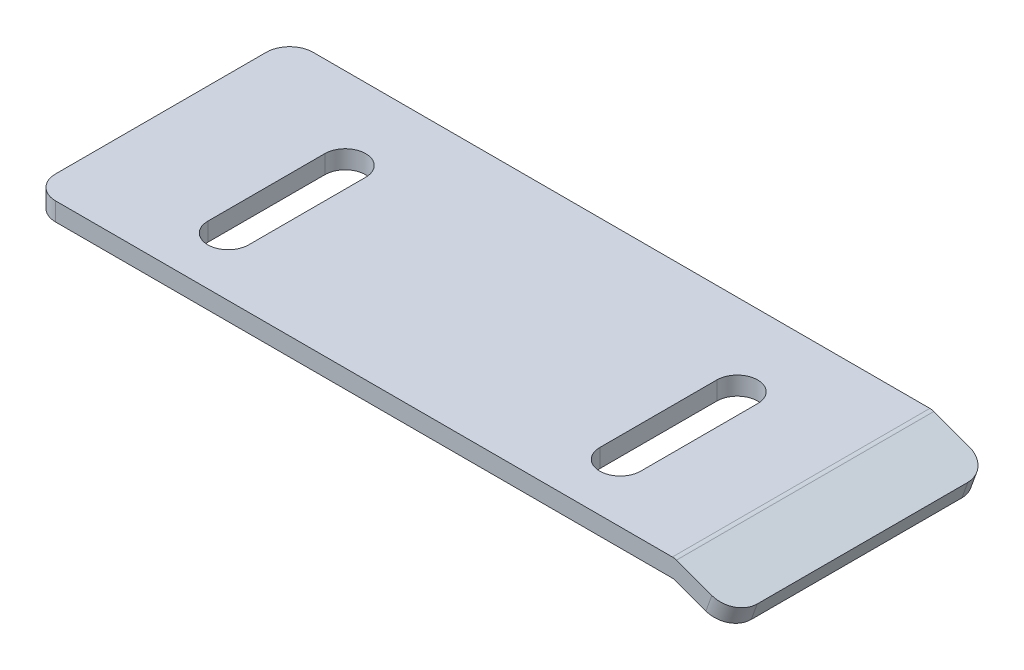
SolidWorks part; units mm, degrees
ref_plane "Front Plane" through (0, 0, 0) normal (0, 0, 1) x (1, 0, 0)
ref_plane "Top Plane" through (0, 0, 0) normal (0, 1, 0) x (1, 0, 0)
ref_plane "Right Plane" through (0, 0, 0) normal (1, 0, 0) x (0, 0, -1)
sketch "Sketch1" plane through (0, 0, 0) normal (0, 0, 1) x (1, 0, 0)
  line L0 (-37.5773, 8.5792) -> (17.3083, 8.5792)
  line L1 (17.3083, 8.5792) -> (22.3827, 6.7323)
  line L2 (22.3827, 6.7323) -> (21.8696, 5.3228)
  line L3 (21.8696, 5.3228) -> (17.2227, 7.0141)
  line L4 (17.2227, 7.0141) -> (-37.5773, 7.0141)
  line L5 (-37.5773, 7.0141) -> (-37.5773, 8.5792)
  dimension "D1" = 5.4
  dimension "D2" = 20
  dimension "D3" = 54.8
  dimension "D4" = 1.5
  dimension "D5" = 59.96
extrude "Boss-Extrude1" add sketch "Sketch1" along normal blind 22
fillet "Fillet1" radius 1 1 edges at (17.3083, 8.5792, 11)
fillet "Fillet2" radius 2 4 edges at (-37.5773, 7.7967, 22) (-37.5773, 7.7967, 0) (22.1261, 6.0276, 22) (22.1261, 6.0276, 0)
sketch "Sketch3" plane through (0, 8.5792, 0) normal (0, 1, 0) x (1, 0, 0)
  line L0 (-37.5773, -20) -> (-37.5773, -2) construction
  line L1 (-35.5773, 0) -> (17.2227, 0) construction
  line L2 (-24.0773, -17) -> (-24.0773, -7)
  line L4 (-27.5773, -17) -> (-27.5773, -7)
  line L6 (9.4227, -17) -> (9.4227, -7)
  line L8 (5.9227, -17) -> (5.9227, -7)
  arc A0 (-27.5773, -17) -> (-24.0773, -17) centre (-25.8273, -17) ccw
  arc A1 (5.9227, -17) -> (9.4227, -17) centre (7.6727, -17) ccw
  arc A2 (9.4227, -7) -> (5.9227, -7) centre (7.6727, -7) ccw
  arc A3 (-24.0773, -7) -> (-27.5773, -7) centre (-25.8273, -7) ccw
  dimension "D1" = 7
  dimension "D2" = 30
  dimension "D3" = 10
  dimension "D4" = 3.5
  dimension "D5" = 3.5
extrude "Cut-Extrude1" cut sketch "Sketch3" against normal through all
